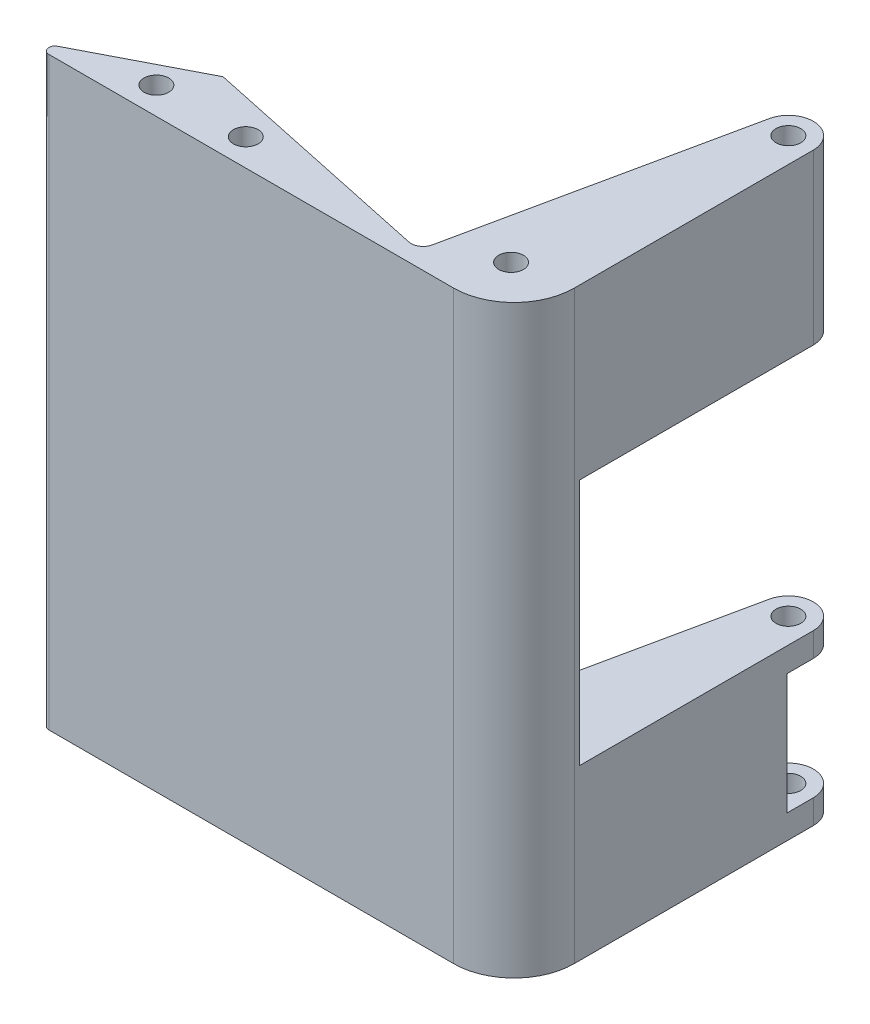
SolidWorks part; units mm, degrees
ref_plane "Front Plane" through (0, 0, 0) normal (0, 0, 1) x (1, 0, 0)
ref_plane "Top Plane" through (0, 0, 0) normal (0, 1, 0) x (1, 0, 0)
ref_plane "Right Plane" through (0, 0, 0) normal (1, 0, 0) x (0, 0, -1)
sketch "Sketch1" plane through (0, 0, 0) normal (0, 1, 0) x (1, 0, 0)
  line L0 (-1.9563, 0.4158) -> (-41.0822, 8.7323)
  line L1 (0.4158, 1.9563) -> (7.9214, 37.2674)
  line L2 (0, 0) -> (21.3798, 0) construction
  line L3 (-41.0822, 8.7323) -> (-58, 0)
  line L4 (-88, -4) -> (-88, 64.58) construction
  line L5 (-88, 64.58) -> (-19.42, 64.58) construction
  line L6 (-41.0822, 8.7323) -> (-33.5766, 44.0434) construction
  line L7 (7.9214, 37.2674) -> (7.9214, -2.5) construction
  line L8 (7.9214, -2.5) -> (-58.7258, -2.5)
  line L9 (-59.1845, -0.6114) -> (-58, 0)
  line L10 (7.9214, -2.5) -> (16.0089, 35.5484) construction
  line L12 (10.0006, 47.0489) -> (-19.4662, 62.063) construction
  line L13 (16.0089, 35.5484) -> (18.2868, 46.273) construction
  line L14 (-19.4662, 62.063) -> (-17.6502, 65.627)
  line L15 (-17.6502, 65.627) -> (11.8165, 50.6129) construction
  line L16 (11.8165, 50.6129) -> (10.0006, 47.0489) construction
  line L17 (11.9637, 36.4087) -> (15.6802, 53.8935) construction
  line L18 (10.9085, 48.8309) -> (22.7332, 42.8059) construction
  line L19 (7.9214, 37.2674) -> (10.1991, 47.9909)
  line L20 (18.377, 47.1319) -> (18.377, 7.5)
  line L21 (8.377, -2.5) -> (7.9214, -2.5)
  circle A0 centre (-88, 64.58) radius 68.58 construction
  circle A1 centre (7.9214, 17.3837) radius 4.1341 construction
  arc A2 (-59.1845, -0.6114) -> (-58.7258, -2.5) centre (-58.7258, -1.5) ccw
  arc A4 (18.377, 47.1319) -> (10.1991, 47.9909) centre (14.243, 47.1319) ccw
  arc A5 (0.4158, 1.9563) -> (-1.9563, 0.4158) centre (-1.5405, 2.3721) cw
  arc A7 (18.377, 7.5) -> (8.377, -2.5) centre (8.377, 7.5) cw
  point P32 (0, 0)
  dimension "D11" = 1
  dimension "D13" = 8.2681
  dimension "D14" = 8.2681
  dimension "D15" = 2
  dimension "D10" = 8.2681
  dimension "D16" = 10
  dimension "D1" = 38.1
  dimension "D2" = 42
  dimension "D3" = 78
  dimension "D4" = 58
  dimension "D5" = 68.58
  dimension "D6" = 4
  dimension "D7" = 1.5
  dimension "D8" = 88
  dimension "D9" = 10
  dimension "D12" = 4
extrude "Boss-Extrude1" add sketch "Sketch1" along normal blind 97 contours L0 L3 L9 A2 L8 L21 A7 L20 A4 L19 L1 A5
sketch "Sketch2" plane through (0, 97, 0) normal (0, 1, 0) x (1, 0, 0)
  line L0 (-45.407, 6.5) -> (-45.407, -2.5) construction
  line L2 (1.6195, 7.6191) -> (9.4447, 5.9558) construction
  line L5 (0.4158, 1.9563) -> (7.9214, 37.2674) construction
  line L6 (-41.0822, 8.7323) -> (-59.1845, -0.6114) construction
  line L7 (8.377, -2.5) -> (-58.7258, -2.5) construction
  line L8 (-30.5801, 6.5) -> (-30.5801, -2.5) construction
  line L9 (-1.9563, 0.4158) -> (-41.0822, 8.7323) construction
  circle A0 centre (-45.407, 2) radius 2.05
  circle A2 centre (9.4447, 5.9558) radius 2.05
  circle A3 centre (14.243, 47.1319) radius 2.05
  circle A4 centre (-30.5801, 2) radius 2.05
  point P23 (-44.7387, 2.1725)
  point P24 (-32.2029, 2.1725)
  point P25 (9.4447, 5.9558)
  dimension "D1" = 4.1
  dimension "D2" = 8
  dimension "D3" = 4.1
  dimension "D4" = 4.1
  dimension "D5" = 4.5
extrude "Cut-Extrude1" cut sketch "Sketch2" against normal through all
ref_plane "Plane1" through (-9.7815, 0, -2.0791) normal (-0.9781, 0, -0.2079) x (-0.2079, 0, 0.9781)
sketch "Sketch5" plane through (-9.7815, 0, -2.0791) normal (-0.9781, 0, -0.2079) x (-0.2079, 0, 0.9781)
  line L0 (-53.1973, 97) -> (-53.1973, 0) construction
  line L1 (-53.1973, 69) -> (-12, 69)
  line L2 (-53.1973, 69) -> (-53.1973, 28)
  line L3 (-53.1973, 28) -> (-12, 28)
  line L4 (-12, 69) -> (-12, 28)
  line L5 (-53.1973, 97) -> (-53.1973, 69)
  line L6 (-53.1973, 28) -> (-53.1973, 0)
  line L7 (0, 97) -> (0, 0) construction
  dimension "D1" = 12
  dimension "D2" = 28
extrude "Cut-Extrude2" cut sketch "Sketch5" against normal through all both and the other way through all contours L4 L1 L2 L3
sketch "Sketch6" plane through (0, 0, 0) normal (0, -1, 0) x (1, 0, 0)
  circle A0 centre (14.243, -47.1319) radius 6
  circle M3 centre (14.243, -47.1319) radius 2.05
  line M7 (7.9214, -37.2674) -> (10.1991, -47.9909)
  arc M8 (10.1991, -47.9909) -> (18.377, -47.1319) centre (14.243, -47.1319) ccw
  line M9 (18.377, -47.1319) -> (18.377, -7.5)
  dimension "D1" = 12
extrude "Cut-Extrude4" cut sketch "Sketch6" against normal blind 20 from offset 4 contours A0 M9 M7 M8 M3 | A0 M7 M9 M8
